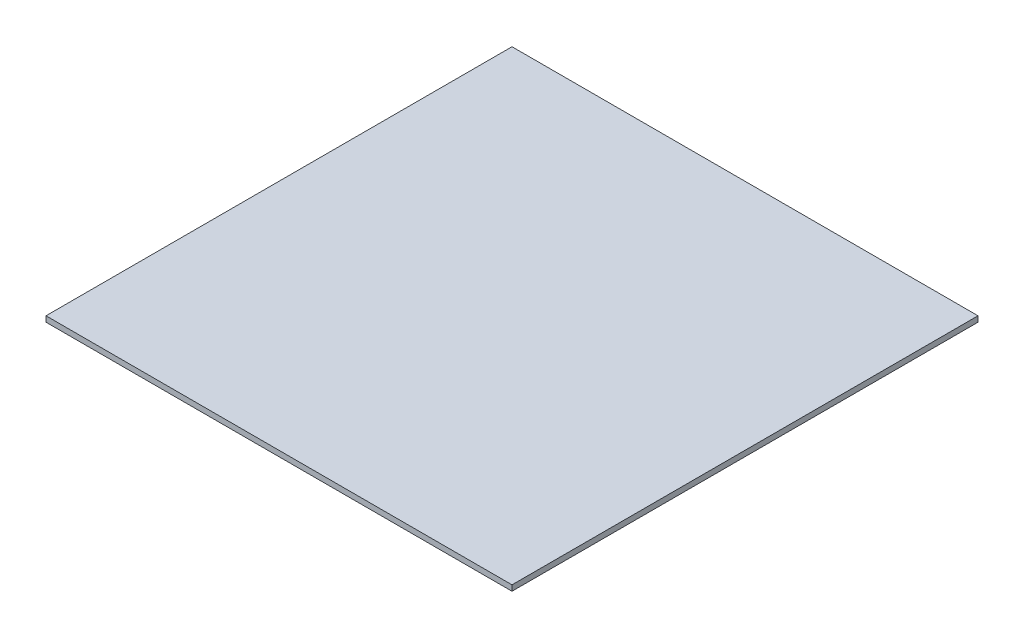
SolidWorks part; units mm, degrees
ref_plane "Ebene vorne" through (0, 0, 0) normal (0, 0, 1) x (1, 0, 0)
ref_plane "Ebene oben" through (0, 0, 0) normal (0, 1, 0) x (1, 0, 0)
ref_plane "Ebene rechts" through (0, 0, 0) normal (1, 0, 0) x (0, 0, -1)
sketch "Sketch1" plane through (0, 0, 0) normal (0, 1, 0) x (1, 0, 0)
  line L1 (-250, -250) -> (250, -250)
  line L2 (-250, -250) -> (-250, 250)
  line L3 (-250, 250) -> (250, 250)
  line L4 (250, -250) -> (250, 250)
  line L5 (-250, -250) -> (250, 250) construction
  line L6 (-250, 250) -> (250, -250) construction
  point P0 (0, 0)
  dimension "D1" = 500
  dimension "D2" = 500
extrude "Boss-Extrude1" add sketch "Sketch1" along normal blind 6
